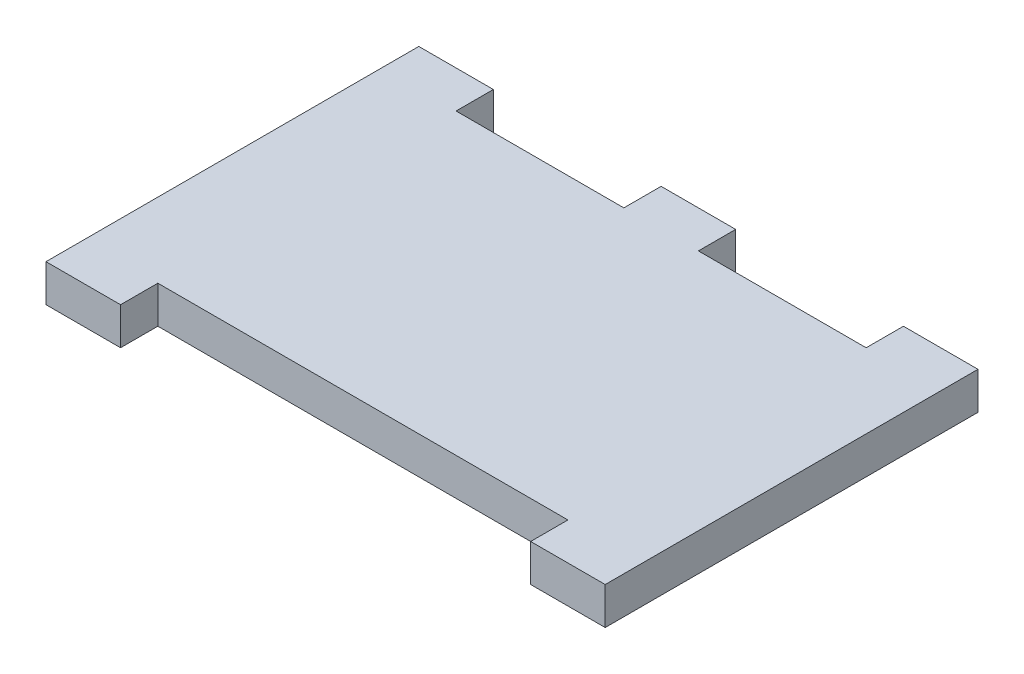
SolidWorks part; units mm, degrees
ref_plane "Front Plane" through (0, 0, 0) normal (0, 0, 1) x (1, 0, 0)
ref_plane "Top Plane" through (0, 0, 0) normal (0, 1, 0) x (1, 0, 0)
ref_plane "Right Plane" through (0, 0, 0) normal (1, 0, 0) x (0, 0, -1)
sketch "Sketch1" plane through (0, 0, 0) normal (0, 1, 0) x (1, 0, 0)
  line L1 (0, 0) -> (114.3, 0)
  line L2 (0, 0) -> (0, 76.2)
  line L3 (0, 76.2) -> (114.3, 76.2)
  line L4 (114.3, 0) -> (114.3, 76.2)
  dimension "D1" = 76.2
  dimension "D2" = 114.3
extrude "Boss-Extrude1" add sketch "Sketch1" along normal blind 7.62 contours L2 L3 L4 L1
sketch "Sketch2" plane through (0, 7.62, 0) normal (0, 1, 0) x (1, 0, 0)
  line L0 (15.24, 76.2) -> (15.24, 0) construction
  line L1 (0, 76.2) -> (114.3, 76.2) construction
  line L2 (0, 0) -> (114.3, 0) construction
  line L3 (99.06, 76.2) -> (99.06, 0) construction
  line L4 (0, 0) -> (0, 76.2) construction
  line L5 (114.3, 0) -> (114.3, 76.2) construction
  line L6 (57.15, 76.2) -> (57.15, 0) construction
  line L12 (15.24, 0) -> (99.06, 0)
  line L13 (15.24, 0) -> (15.24, 7.62)
  line L14 (49.53, 76.2) -> (15.24, 76.2)
  line L15 (49.53, 76.2) -> (49.53, 68.58)
  line L16 (49.53, 68.58) -> (15.24, 68.58)
  line L17 (15.24, 76.2) -> (15.24, 68.58)
  line L18 (64.77, 68.58) -> (99.06, 68.58)
  line L19 (64.77, 68.58) -> (64.77, 76.2)
  line L20 (64.77, 76.2) -> (99.06, 76.2)
  line L21 (99.06, 68.58) -> (99.06, 76.2)
  line L22 (15.24, 7.62) -> (99.06, 7.62)
  line L23 (99.06, 0) -> (99.06, 7.62)
  point P14 (57.15, 72.39)
  dimension "D1" = 15.24
  dimension "D2" = 15.24
  dimension "D3" = 15.24
  dimension "D4" = 7.62
  dimension "D5" = 7.62
extrude "Cut-Extrude1" cut sketch "Sketch2" against normal through all
equation "\"MDF\" = 0.3in"
equation "\"TopPlatformHeight\" = 3in"
equation "\"D1@Sketch1\"=\"TopPlatformHeight\""
equation "\"D1@Boss-Extrude1\"=\"MDF\""
equation "\"D4@Sketch2\"=\"MDF\""
equation "\"D5@Sketch2\"=\"MDF\""
